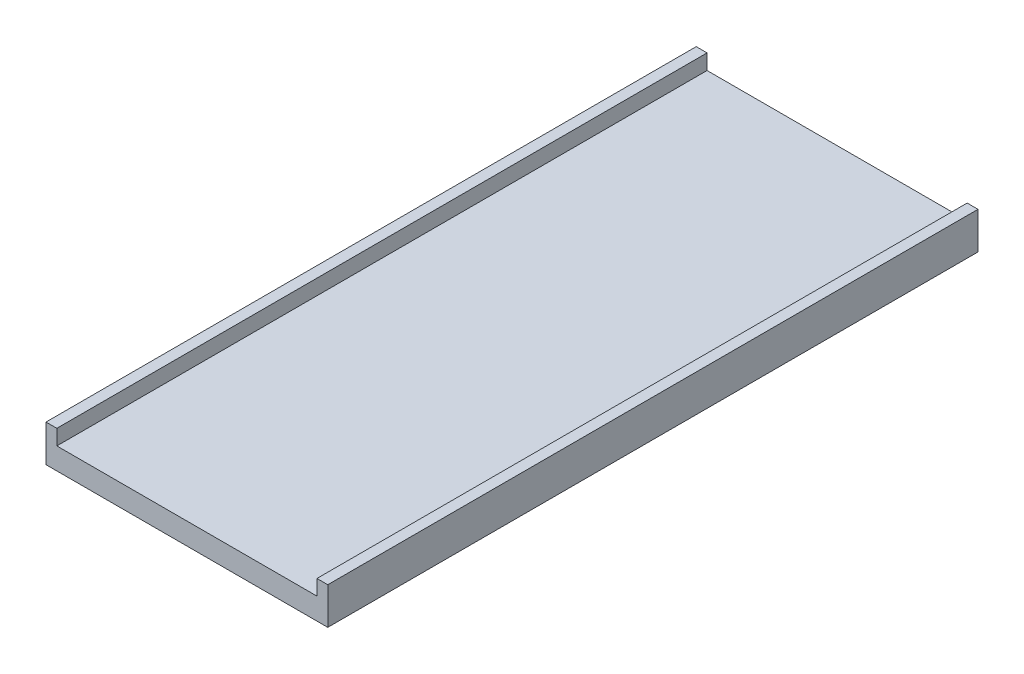
SolidWorks part; units mm, degrees
ref_plane "Front Plane" through (0, 0, 0) normal (0, 0, 1) x (1, 0, 0)
ref_plane "Top Plane" through (0, 0, 0) normal (0, 1, 0) x (1, 0, 0)
ref_plane "Right Plane" through (0, 0, 0) normal (1, 0, 0) x (0, 0, -1)
sketch "Sketch1" plane through (0, 0, 0) normal (0, 0, 1) x (1, 0, 0)
  line L0 (0, 0) -> (25, 0)
  line L1 (25, 0) -> (25, -35.2361)
  line L2 (25, -35.2361) -> (625, -35.2361)
  line L3 (625, -35.2361) -> (625, 0)
  line L4 (625, 0) -> (650, 0)
  line L5 (650, 0) -> (650, -85.2361)
  line L6 (650, -85.2361) -> (0, -85.2361)
  line L7 (0, -85.2361) -> (0, 0)
  line L8 (-2000, 0) -> (-2000, 547.1361)
  dimension "D1" = 25
  dimension "D2" = 35.2361
  dimension "D3" = 650
  dimension "D4" = 50
  dimension "D5" = 2000
extrude "Boss-Extrude1" add sketch "Sketch1" along normal blind 1500 contours L2 L3 L4 L5 L6 L7 L0 L1
